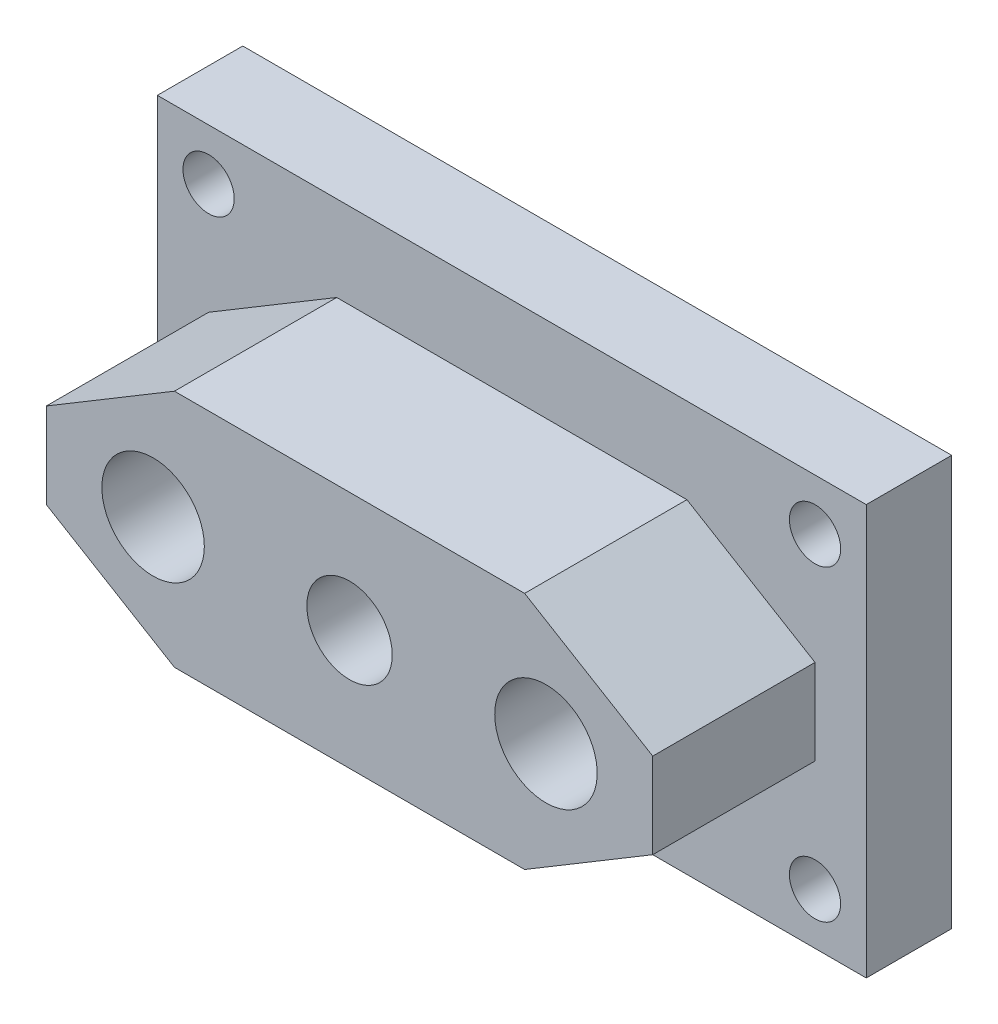
SolidWorks part; units mm, degrees
ref_plane "Front Plane" through (0, 0, 0) normal (0, 0, 1) x (1, 0, 0)
ref_plane "Top Plane" through (0, 0, 0) normal (0, 1, 0) x (1, 0, 0)
ref_plane "Right Plane" through (0, 0, 0) normal (1, 0, 0) x (0, 0, -1)
sketch "Sketch1" plane through (0, 0, 0) normal (0, 0, 1) x (1, 0, 0)
  line L1 (-41.5, -24) -> (41.5, -24)
  line L2 (-41.5, -24) -> (-41.5, 24)
  line L3 (-41.5, 24) -> (41.5, 24)
  line L4 (41.5, -24) -> (41.5, 24)
  line L5 (-41.5, -24) -> (41.5, 24) construction
  line L6 (-41.5, 24) -> (41.5, -24) construction
  point P0 (0, 0)
  dimension "D1" = 48
  dimension "D2" = 83
extrude "Boss-Extrude1" add sketch "Sketch1" along normal blind 10
sketch "Sketch2" plane through (0, 0, 10) normal (0, 0, 1) x (1, 0, 0)
  line L0 (-35.5, 5) -> (-20.5, 14)
  line L1 (-20.5, -14) -> (20.5, -14)
  line L2 (-35.5, -5) -> (-35.5, 5)
  line L3 (-20.5, 14) -> (20.5, 14)
  line L4 (35.5, -5) -> (35.5, 5)
  line L5 (-35.5, -14) -> (35.5, 14) construction
  line L6 (-35.5, 14) -> (35.5, -14) construction
  line L7 (0, 17.6868) -> (0, -19.7187) construction
  line L8 (-40.1763, 0) -> (38.6985, 0) construction
  line L9 (35.5, 5) -> (20.5, 14)
  line L10 (35.5, -5) -> (20.5, -14)
  line L11 (-35.5, -5) -> (-20.5, -14)
  point P0 (0, 0)
  dimension "D1" = 28
  dimension "D2" = 71
  dimension "D3" = 15
  dimension "D4" = 9
extrude "Boss-Extrude2" add sketch "Sketch2" along normal blind 19
sketch "Sketch3" plane through (0, 0, 29) normal (0, 0, 1) x (1, 0, 0)
  line L0 (-48.581, 0) -> (52.7372, 0) construction
  line L1 (0, 33.3879) -> (0, -34.4962) construction
  line L3 (41.5, 24) -> (-41.5, 24) construction
  circle A0 centre (0, 0) radius 5
  circle A1 centre (-23, 0) radius 6
  circle A2 centre (23, 0) radius 6
  circle A3 centre (-35.5, 18) radius 3
  circle A4 centre (35.5, 18) radius 3
  circle A5 centre (35.5, -18) radius 3
  circle A6 centre (-35.5, -18) radius 3
  dimension "D1" = 10
  dimension "D2" = 12
  dimension "D5" = 6
  dimension "D3" = 23
  dimension "D4" = 35.5
  dimension "D6" = 18
  dimension "D7" = 6
extrude "Cut-Extrude1" cut sketch "Sketch3" against normal through all
